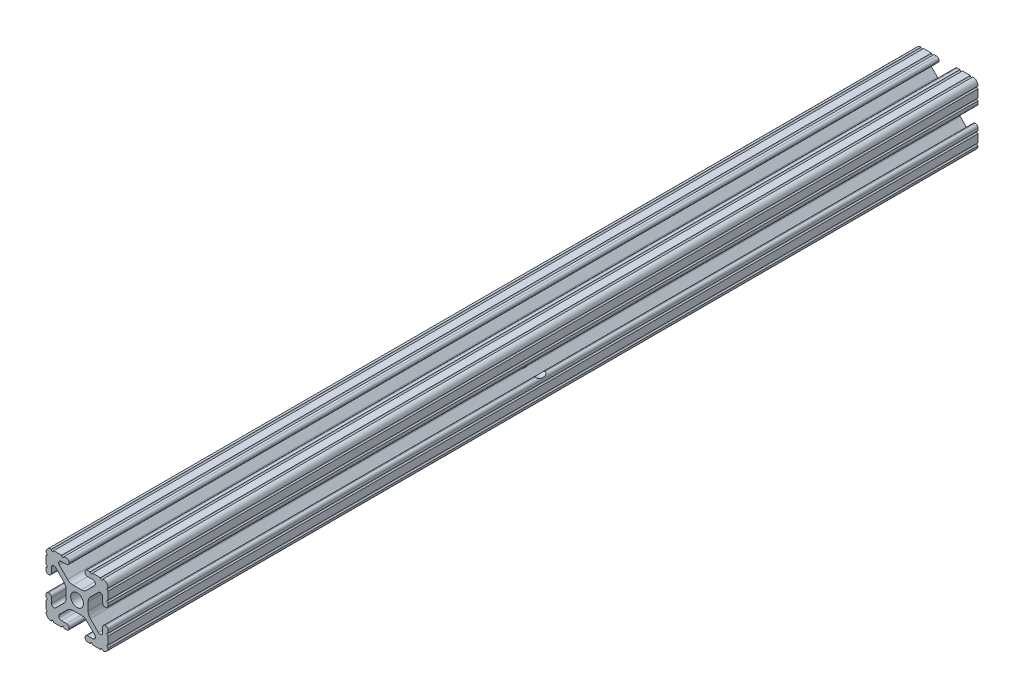
SolidWorks part; units mm, degrees
ref_plane "Front Plane" through (0, 0, 0) normal (0, 0, 1) x (1, 0, 0)
ref_plane "Top Plane" through (0, 0, 0) normal (0, 1, 0) x (1, 0, 0)
ref_plane "Right Plane" through (0, 0, 0) normal (1, 0, 0) x (0, 0, -1)
sketch "Sketch1" plane through (0, 0, 0) normal (0, 0, 1) x (1, 0, 0)
  line L88 (-7.1797, -8.6452) -> (-3.9523, -5.4237)
  line L89 (-1.7093, -4.4958) -> (1.7093, -4.4958)
  line L90 (3.9523, -5.4237) -> (7.1797, -8.6452)
  line L91 (6.4164, -10.4902) -> (4.2875, -10.4902)
  line L92 (3.2385, -11.5392) -> (3.2385, -11.651)
  line L93 (4.2875, -12.7) -> (5.3171, -12.7)
  line L94 (6.3331, -12.7) -> (9.5504, -12.7)
  line L95 (12.7, -9.5504) -> (12.7, -6.3331)
  line L96 (12.7, -5.3171) -> (12.7, -4.2875)
  line L97 (11.651, -3.2385) -> (11.5392, -3.2385)
  line L98 (10.4902, -4.2875) -> (10.4902, -6.4021)
  line L99 (8.7371, -7.1294) -> (5.441, -3.8408)
  line L100 (4.5085, -1.5932) -> (4.5085, 1.5932)
  line L101 (5.441, 3.8408) -> (8.7371, 7.1294)
  line L102 (10.4902, 6.4021) -> (10.4902, 4.2875)
  line L103 (11.5392, 3.2385) -> (11.651, 3.2385)
  line L104 (12.7, 4.2875) -> (12.7, 5.3171)
  line L105 (12.7, 6.3331) -> (12.7, 9.5504)
  line L106 (9.5504, 12.7) -> (6.3331, 12.7)
  line L107 (5.3171, 12.7) -> (4.2875, 12.7)
  line L108 (3.2385, 11.651) -> (3.2385, 11.5392)
  line L109 (4.2875, 10.4902) -> (6.4768, 10.4902)
  line L110 (7.207, 8.7244) -> (3.8983, 5.4232)
  line L111 (1.6558, 4.4958) -> (-1.6558, 4.4958)
  line L112 (-3.8983, 5.4232) -> (-7.207, 8.7244)
  line L113 (-6.4768, 10.4902) -> (-4.2875, 10.4902)
  line L114 (-3.2385, 11.5392) -> (-3.2385, 11.651)
  line L115 (-4.2875, 12.7) -> (-5.3171, 12.7)
  line L116 (-6.3331, 12.7) -> (-9.5504, 12.7)
  line L117 (-12.7, 9.5504) -> (-12.7, 6.3331)
  line L118 (-12.7, 5.3171) -> (-12.7, 4.2875)
  line L119 (-11.651, 3.2385) -> (-11.5392, 3.2385)
  line L120 (-10.4902, 4.2875) -> (-10.4902, 6.4021)
  line L121 (-8.7371, 7.1294) -> (-5.441, 3.8408)
  line L122 (-4.5085, 1.5932) -> (-4.5085, -1.5932)
  line L123 (-5.441, -3.8408) -> (-8.7371, -7.1294)
  line L124 (-10.4902, -6.4021) -> (-10.4902, -4.2875)
  line L125 (-11.5392, -3.2385) -> (-11.651, -3.2385)
  line L126 (-12.7, -4.2875) -> (-12.7, -5.3171)
  line L127 (-12.7, -6.3331) -> (-12.7, -9.5504)
  line L128 (-9.5504, -12.7) -> (-6.3331, -12.7)
  line L129 (-5.3171, -12.7) -> (-4.2875, -12.7)
  line L130 (-3.2385, -11.651) -> (-3.2385, -11.5392)
  line L131 (-4.2875, -10.4902) -> (-6.4164, -10.4902)
  circle A1 centre (0, 0) radius 2.6035
  arc A104 (-7.1797, -8.6452) -> (-6.4164, -10.4902) centre (-6.4164, -9.4098) ccw
  arc A105 (-1.7093, -4.4958) -> (-3.9523, -5.4237) centre (-1.7093, -7.6708) ccw
  arc A106 (3.9523, -5.4237) -> (1.7093, -4.4958) centre (1.7093, -7.6708) ccw
  arc A107 (6.4164, -10.4902) -> (7.1797, -8.6452) centre (6.4164, -9.4098) ccw
  arc A108 (4.2875, -10.4902) -> (3.2385, -11.5392) centre (4.2875, -11.5392) ccw
  arc A109 (3.2385, -11.651) -> (4.2875, -12.7) centre (4.2875, -11.651) ccw
  arc A110 (6.3331, -12.7) -> (5.3171, -12.7) centre (5.8251, -12.7) ccw
  arc A111 (10.5664, -12.6998) -> (9.5504, -12.7) centre (10.0584, -12.7) ccw
  arc A112 (10.5664, -12.6998) -> (12.6998, -10.5664) centre (10.5918, -10.5918) ccw
  arc A113 (12.7, -9.5504) -> (12.6998, -10.5664) centre (12.7, -10.0584) ccw
  arc A114 (12.7, -5.3171) -> (12.7, -6.3331) centre (12.7, -5.8251) ccw
  arc A115 (12.7, -4.2875) -> (11.651, -3.2385) centre (11.651, -4.2875) ccw
  arc A116 (11.5392, -3.2385) -> (10.4902, -4.2875) centre (11.5392, -4.2875) ccw
  arc A117 (8.7371, -7.1294) -> (10.4902, -6.4021) centre (9.4628, -6.4021) ccw
  arc A118 (4.5085, -1.5932) -> (5.441, -3.8408) centre (7.6835, -1.5932) ccw
  arc A119 (5.441, 3.8408) -> (4.5085, 1.5932) centre (7.6835, 1.5932) ccw
  arc A120 (10.4902, 6.4021) -> (8.7371, 7.1294) centre (9.4628, 6.4021) ccw
  arc A121 (10.4902, 4.2875) -> (11.5392, 3.2385) centre (11.5392, 4.2875) ccw
  arc A122 (11.651, 3.2385) -> (12.7, 4.2875) centre (11.651, 4.2875) ccw
  arc A123 (12.7, 6.3331) -> (12.7, 5.3171) centre (12.7, 5.8251) ccw
  arc A124 (12.6998, 10.5664) -> (12.7, 9.5504) centre (12.7, 10.0584) ccw
  arc A125 (12.6998, 10.5664) -> (10.5664, 12.6998) centre (10.5918, 10.5918) ccw
  arc A126 (9.5504, 12.7) -> (10.5664, 12.6998) centre (10.0584, 12.7) ccw
  arc A127 (5.3171, 12.7) -> (6.3331, 12.7) centre (5.8251, 12.7) ccw
  arc A128 (4.2875, 12.7) -> (3.2385, 11.651) centre (4.2875, 11.651) ccw
  arc A129 (3.2385, 11.5392) -> (4.2875, 10.4902) centre (4.2875, 11.5392) ccw
  arc A130 (7.207, 8.7244) -> (6.4768, 10.4902) centre (6.4768, 9.4563) ccw
  arc A131 (1.6558, 4.4958) -> (3.8983, 5.4232) centre (1.6558, 7.6708) ccw
  arc A132 (-3.8983, 5.4232) -> (-1.6558, 4.4958) centre (-1.6558, 7.6708) ccw
  arc A133 (-6.4768, 10.4902) -> (-7.207, 8.7244) centre (-6.4768, 9.4563) ccw
  arc A134 (-4.2875, 10.4902) -> (-3.2385, 11.5392) centre (-4.2875, 11.5392) ccw
  arc A135 (-3.2385, 11.651) -> (-4.2875, 12.7) centre (-4.2875, 11.651) ccw
  arc A136 (-6.3331, 12.7) -> (-5.3171, 12.7) centre (-5.8251, 12.7) ccw
  arc A137 (-10.5664, 12.6998) -> (-9.5504, 12.7) centre (-10.0584, 12.7) ccw
  arc A138 (-10.5664, 12.6998) -> (-12.6998, 10.5664) centre (-10.5918, 10.5918) ccw
  arc A139 (-12.7, 9.5504) -> (-12.6998, 10.5664) centre (-12.7, 10.0584) ccw
  arc A140 (-12.7, 5.3171) -> (-12.7, 6.3331) centre (-12.7, 5.8251) ccw
  arc A141 (-12.7, 4.2875) -> (-11.651, 3.2385) centre (-11.651, 4.2875) ccw
  arc A142 (-11.5392, 3.2385) -> (-10.4902, 4.2875) centre (-11.5392, 4.2875) ccw
  arc A143 (-8.7371, 7.1294) -> (-10.4902, 6.4021) centre (-9.4628, 6.4021) ccw
  arc A144 (-4.5085, 1.5932) -> (-5.441, 3.8408) centre (-7.6835, 1.5932) ccw
  arc A145 (-5.441, -3.8408) -> (-4.5085, -1.5932) centre (-7.6835, -1.5932) ccw
  arc A146 (-10.4902, -6.4021) -> (-8.7371, -7.1294) centre (-9.4628, -6.4021) ccw
  arc A147 (-10.4902, -4.2875) -> (-11.5392, -3.2385) centre (-11.5392, -4.2875) ccw
  arc A148 (-11.651, -3.2385) -> (-12.7, -4.2875) centre (-11.651, -4.2875) ccw
  arc A149 (-12.7, -6.3331) -> (-12.7, -5.3171) centre (-12.7, -5.8251) ccw
  arc A150 (-12.6998, -10.5664) -> (-12.7, -9.5504) centre (-12.7, -10.0584) ccw
  arc A151 (-12.6998, -10.5664) -> (-10.5664, -12.6998) centre (-10.5918, -10.5918) ccw
  arc A152 (-9.5504, -12.7) -> (-10.5664, -12.6998) centre (-10.0584, -12.7) ccw
  arc A153 (-5.3171, -12.7) -> (-6.3331, -12.7) centre (-5.8251, -12.7) ccw
  arc A154 (-4.2875, -12.7) -> (-3.2385, -11.651) centre (-4.2875, -11.651) ccw
  arc A155 (-3.2385, -11.5392) -> (-4.2875, -10.4902) centre (-4.2875, -11.5392) ccw
extrude "Boss-Extrude1" add sketch "Sketch1" along normal mid plane 355.6
sketch "Sketch2" plane through (-12.7, 0, 0) normal (-1, 0, 0) x (0, 0, 1)
  circle A0 centre (0, 0) radius 3.81
  dimension "D1" = 7.62
extrude "Cut-Extrude1" cut sketch "Sketch2" against normal blind 25.4
sketch "Sketch3" plane through (0, 4.4958, 0) normal (0, 1, 0) x (1, 0, 0)
  line L0 (0, 219.8063) -> (0, -211.9937) construction
  line L3 (0, 0) -> (42.3686, 0) construction
  line L4 (1.6558, -177.8) -> (-1.6558, -177.8) construction
  circle A0 centre (0, -165.1) radius 3.175
  circle A1 centre (0, 165.1) radius 3.175
  dimension "D1" = 6.35
  dimension "D2" = 12.7
extrude "Cut-Extrude2" cut sketch "Sketch3" against normal through all both and the other way through all
